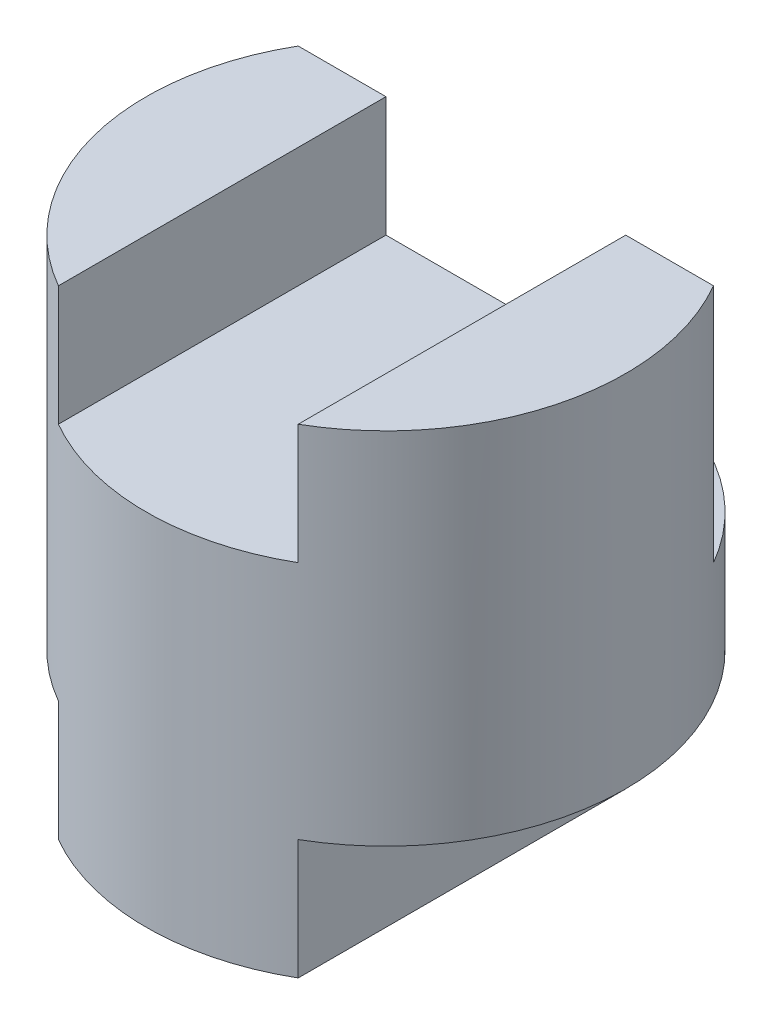
SolidWorks part; units mm, degrees
ref_plane "Front" through (0, 0, 0) normal (0, 0, 1) x (1, 0, 0)
ref_plane "Top" through (0, 0, 0) normal (0, 1, 0) x (1, 0, 0)
ref_plane "Right" through (0, 0, 0) normal (1, 0, 0) x (0, 0, -1)
sketch "Sketch1" plane through (0, 0, 0) normal (0, 1, 0) x (1, 0, 0)
  circle A0 centre (0, 0) radius 2
  dimension "D1" = 4
extrude "Boss-Extrude1" add sketch "Sketch1" along normal blind 4
sketch "Sketch2" plane through (0, 0, 0) normal (0, 0, 1) x (1, 0, 0)
  line L0 (2, 4) -> (-2, 4) construction
  line L2 (-1, 0) -> (-1, 1)
  line L4 (1, 0) -> (1, 1)
  line L5 (1, 4) -> (-1, 4)
  line L6 (1, 4) -> (1, 3)
  line L7 (1, 3) -> (-1, 3)
  line L8 (-1, 4) -> (-1, 3)
  line L9 (2, 0) -> (2, 4) construction
  line L10 (-2, 0) -> (-1, 0)
  line L11 (-2, 0) -> (-2, 1)
  line L12 (-2, 1) -> (-1, 1)
  line L13 (2, 0) -> (2, 1)
  line L14 (1, 1) -> (2, 1)
  line L15 (1, 0) -> (2, 0)
  dimension "D1" = 1
  dimension "D2" = 1
  dimension "D3" = 2
  dimension "D4" = 1
  dimension "D5" = 2
  dimension "D6" = 1
extrude "Cut-Extrude1" cut sketch "Sketch2" against normal mid plane 10 contours L2 L12 L11 L10 | L4 L14 L13 L15 | L6 L5 L8 L7
sketch "Sketch3" plane through (0, 4, 0) normal (0, 1, 0) x (1, 0, 0)
  line L0 (1.7321, 1) -> (-1.7321, 1)
  arc A0 (-1, 1.7321) -> (-1, -1.7321) centre (0, 0) ccw construction
  arc A1 (-1.7321, 1) -> (1.7321, 1) centre (0, 0) cw
  dimension "D1" = 1
extrude "Cut-Extrude2" cut sketch "Sketch3" against normal blind 2
sketch "Sketch4" plane through (0, 0, 0) normal (0, -1, 0) x (1, 0, 0)
  line L0 (1.7321, -1) -> (-1.7321, -1)
  arc A0 (1, -1.7321) -> (1, 1.7321) centre (0, 0) ccw construction
  arc A1 (-1, 1.7321) -> (-1, -1.7321) centre (0, 0) ccw construction
  arc A2 (1.7321, -1) -> (-1.7321, -1) centre (0, 0) cw
  dimension "D1" = 1
extrude "Cut-Extrude3" cut sketch "Sketch4" against normal blind 1
